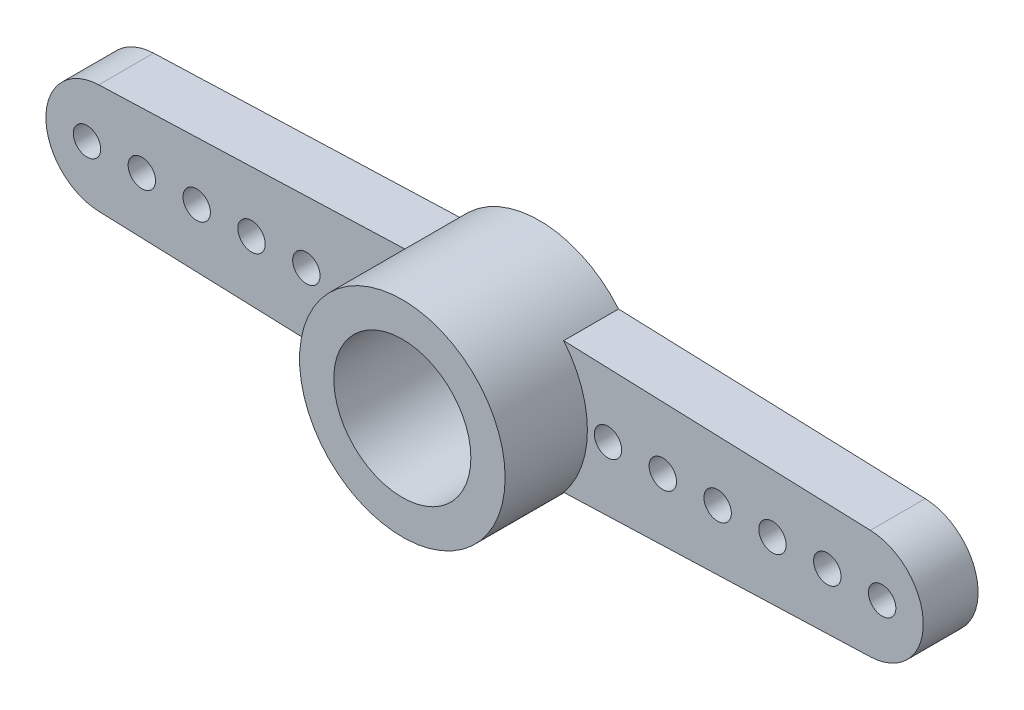
SolidWorks part; units mm, degrees
ref_plane "Спереди" through (0, 0, 0) normal (0, 0, 1) x (1, 0, 0)
ref_plane "Сверху" through (0, 0, 0) normal (0, 1, 0) x (1, 0, 0)
ref_plane "Справа" through (0, 0, 0) normal (1, 0, 0) x (0, 0, -1)
sketch "Эскиз1" plane through (0, 0, 0) normal (0, 0, 1) x (1, 0, 0)
  line L0 (0, 0) -> (-14, 0)
  line L1 (-14.0708, 1.9987) -> (0, 2.4974)
  line L2 (-14.0708, -1.9987) -> (0, -2.4974)
  line L4 (14.0708, -1.9987) -> (0, -2.4974)
  line L5 (14.0708, 1.9987) -> (0, 2.4974)
  circle A0 centre (0, 0) radius 3.75
  circle A1 centre (0, 0) radius 2.5
  arc A2 (-13.967, -1.9997) -> (-14.0708, 1.9987) centre (-14, 0) cw
  arc A3 (13.967, -1.9997) -> (14.0708, 1.9987) centre (14, 0) ccw
  dimension "D1" = 7.5
  dimension "D2" = 5
  dimension "D4" = 2
  dimension "D3" = 14
extrude "Бобышка-Вытянуть3" add sketch "Эскиз1" along normal blind 2
sketch "Эскиз2" plane through (0, 0, 2) normal (0, 0, 1) x (1, 0, 0)
  circle A0 centre (0, 0) radius 3.75
  circle A1 centre (0, 0) radius 2.5
  dimension "D1" = 5
extrude "Бобышка-Вытянуть5" add sketch "Эскиз2" along normal blind 3 separate body
sketch "Эскиз3" plane through (0, 0, 2) normal (0, 0, -1) x (-1, 0, 0)
  circle A0 centre (0, 0) radius 3.75
  circle A1 centre (0, 0) radius 2.5
extrude "Бобышка-Вытянуть6" add sketch "Эскиз3" along normal blind 2
sketch "Эскиз4" plane through (0, 0, 0) normal (0, 0, -1) x (-1, 0, 0)
  line L0 (-16, 0) -> (-14.5, 0)
  line L1 (-14.5, 0) -> (-12.5, 0)
  line L2 (-12.5, 0) -> (-10.5, 0)
  line L3 (-10.5, 0) -> (-8.5, 0)
  line L4 (-8.5, 0) -> (-6.5, 0)
  line L5 (-6.5, 0) -> (-4.5, 0)
  arc A0 (-14.0708, 1.9987) -> (-14.0708, -1.9987) centre (-14, 0) ccw construction
  circle A1 centre (-14.5, 0) radius 0.5
  circle A2 centre (-12.5, 0) radius 0.5
  circle A3 centre (-10.5, 0) radius 0.5
  circle A4 centre (-8.5, 0) radius 0.5
  circle A5 centre (-6.5, 0) radius 0.5
  circle A6 centre (-4.5, 0) radius 0.5
  circle A7 centre (4.5, 0) radius 0.5
  circle A8 centre (6.5, 0) radius 0.5
  circle A9 centre (8.5, 0) radius 0.5
  circle A10 centre (10.5, 0) radius 0.5
  circle A11 centre (12.5, 0) radius 0.5
  circle A12 centre (14.5, 0) radius 0.5
  dimension "D2" = 1
  dimension "D8" = 1
  dimension "D9" = 1
  dimension "D10" = 1
  dimension "D11" = 1
  dimension "D12" = 1
  dimension "D1" = 1.5
  dimension "D3" = 2
  dimension "D4" = 2
  dimension "D5" = 2
  dimension "D6" = 2
  dimension "D7" = 2
extrude "Вырез-Вытянуть1" cut sketch "Эскиз4" against normal blind 2
sketch "Эскиз5" plane through (0, 0, 0) normal (0, 0, -1) x (-1, 0, 0)
  circle A0 centre (0, 0) radius 2.5
extrude "Бобышка-Вытянуть7" add sketch "Эскиз5" against normal blind 1
sketch "Эскиз6" plane through (0, 0, 0) normal (0, 0, -1) x (-1, 0, 0)
  circle A0 centre (0, 0) radius 2.5
  dimension "D1" = 5
extrude "Вырез-Вытянуть2" cut sketch "Эскиз6" against normal blind 0.5
sketch "Эскиз7" plane through (0, 0, 0.5) normal (0, 0, -1) x (-1, 0, 0)
  circle A0 centre (0, 0) radius 1.25
  dimension "D1" = 2.5
extrude "Вырез-Вытянуть3" cut sketch "Эскиз7" against normal blind 5
sketch "Эскиз8" plane through (0, 0, 0.5) normal (0, 0, -1) x (-1, 0, 0)
  line L0 (-2.8252, -0.1999) -> (-2.8894, -0.2509)
sketch "Sketch1" plane through (0, 0, 5) normal (0, 0, 1) x (1, 0, 0)
  line L2 (2.8855, -2.3951) -> (14.0708, -1.9987)
  line L3 (14.0708, 1.9987) -> (2.8855, 2.3951)
  line L4 (2.8855, -2.3951) -> (14.0708, -1.9987)
  line L5 (14.0708, 1.9987) -> (2.8855, 2.3951)
  arc A0 (2.8855, -2.3951) -> (2.8855, 2.3951) centre (0, 0) ccw
  arc A3 (2.8855, -2.3951) -> (2.8855, 2.3951) centre (0, 0) ccw
  arc A4 (14.0708, -1.9987) -> (14.0708, 1.9987) centre (14, 0) ccw
  arc A5 (2.8855, -2.3951) -> (2.8855, 2.3951) centre (0, 0) ccw
  arc A6 (14.0708, -1.9987) -> (14.0708, 1.9987) centre (14, 0) ccw
  dimension "D1" = 0
